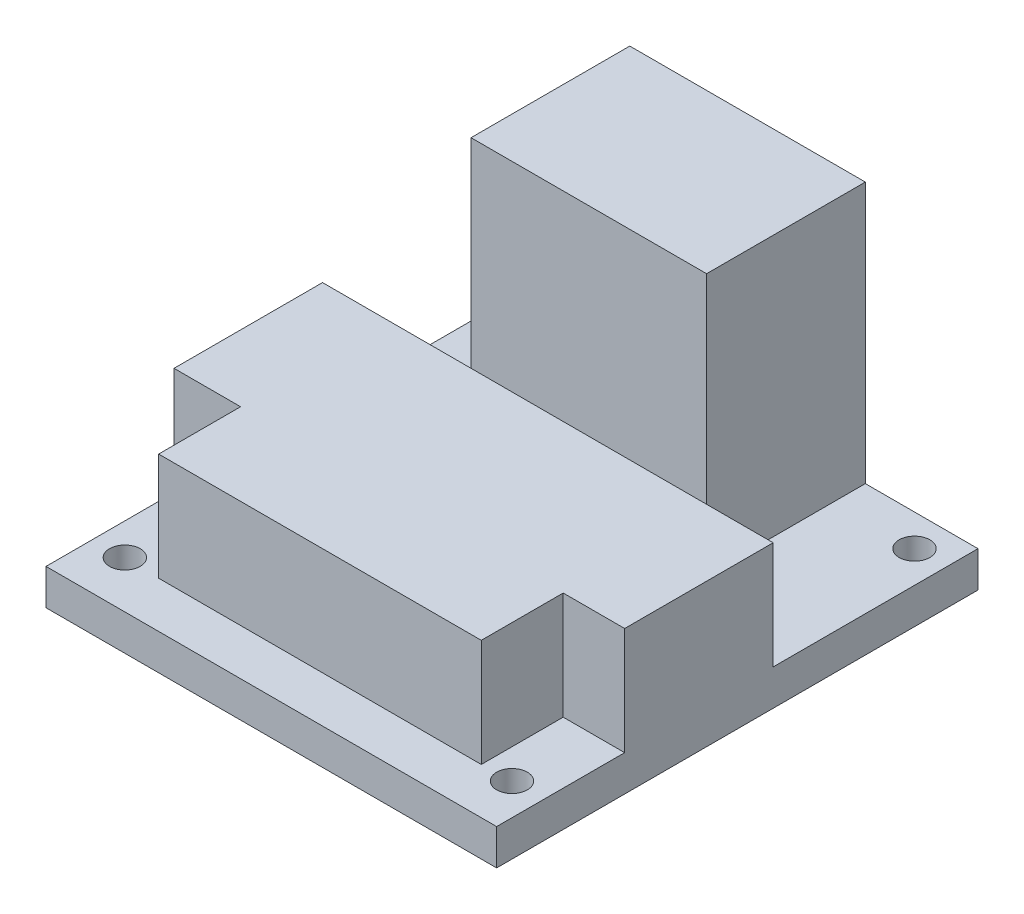
SolidWorks part; units mm, degrees
ref_plane "Front Plane" through (0, 0, 0) normal (0, 0, 1) x (1, 0, 0)
ref_plane "Top Plane" through (0, 0, 0) normal (0, 1, 0) x (1, 0, 0)
ref_plane "Right Plane" through (0, 0, 0) normal (1, 0, 0) x (0, 0, -1)
sketch "Sketch2" plane through (0, 0, 0) normal (0, 1, 0) x (1, 0, 0)
  line L1 (0, 0) -> (44, 0)
  line L2 (0, 0) -> (0, 47)
  line L3 (0, 47) -> (44, 47)
  line L4 (44, 0) -> (44, 47)
  dimension "D1" = 44
  dimension "D2" = 47
extrude "Boss-Extrude1" add sketch "Sketch2" along normal blind 3.5
sketch "Sketch3" plane through (0, 3.5, 0) normal (0, 1, 0) x (1, 0, 0)
  line L0 (0, 0) -> (44, 0) construction
  line L2 (0, 4.5) -> (44, 4.5)
  line L3 (0, 4.5) -> (0, 27)
  line L4 (0, 27) -> (44, 27)
  line L5 (44, 4.5) -> (44, 27)
  line L6 (0, 47) -> (0, 0) construction
  line L8 (44, 0) -> (44, 47) construction
  dimension "D1" = 4.5
  dimension "D2" = 22.5
extrude "Boss-Extrude2" add sketch "Sketch3" along normal blind 10.5
sketch "Sketch4" plane through (0, 3.5, 0) normal (0, 1, 0) x (1, 0, 0)
  line L0 (44, 47) -> (0, 47) construction
  line L1 (10, 47) -> (33, 47)
  line L2 (10, 47) -> (10, 31.5)
  line L3 (10, 31.5) -> (33, 31.5)
  line L4 (33, 47) -> (33, 31.5)
  line L5 (44, 27) -> (44, 47) construction
  line L6 (0, 47) -> (0, 27) construction
  dimension "D1" = 11
  dimension "D2" = 10
  dimension "D3" = 15.5
extrude "Boss-Extrude3" add sketch "Sketch4" along normal blind 25.5
sketch "Sketch5" plane through (0, 14, 0) normal (0, 1, 0) x (1, 0, 0)
  line L0 (0, 0) -> (44, 0) construction
  line L1 (0, 4.5) -> (6.5, 4.5)
  line L2 (0, 4.5) -> (0, 12.5)
  line L3 (0, 12.5) -> (6.5, 12.5)
  line L4 (6.5, 4.5) -> (6.5, 12.5)
  line L6 (44, 4.5) -> (38, 4.5)
  line L7 (44, 4.5) -> (44, 12.5)
  line L8 (44, 12.5) -> (38, 12.5)
  line L9 (38, 4.5) -> (38, 12.5)
  dimension "D1" = 12.5
  dimension "D2" = 6.5
  dimension "D3" = 6
  dimension "D4" = 12.5
extrude "Cut-Extrude1" cut sketch "Sketch5" against normal up to surface (10.5 mm away) up to face at (22, 3.5, -2.25)
sketch "Sketch6" plane through (0, 0, 0) normal (0, 1, 0) x (1, 0, 0)
  line L0 (10, 47) -> (0, 47) construction
  line L1 (0, 47) -> (0, 27) construction
  line L2 (3.1, 43.9) -> (38.8448, 43.9) construction
  line L3 (44, 27) -> (44, 47) construction
  line L4 (40.9, 43.9) -> (40.9, 3.3102) construction
  line L5 (3.1, 43.9) -> (3.1, 7.2086) construction
  line L6 (0, 0) -> (44, 0) construction
  line L7 (3.1, 4.6) -> (40.9, 4.6) construction
  circle A0 centre (3.1, 43.9) radius 1.5
  circle A1 centre (40.9, 43.9) radius 1.5
  circle A2 centre (40.9, 4.6) radius 1.5
  circle A3 centre (3.1, 4.6) radius 1.5
  dimension "D1" = 3.1
  dimension "D2" = 3
  dimension "D4" = 3.1
  dimension "D5" = 4.6
  dimension "D3" = 3.1
extrude "Cut-Extrude3" cut sketch "Sketch6" against normal through all both and the other way through all
